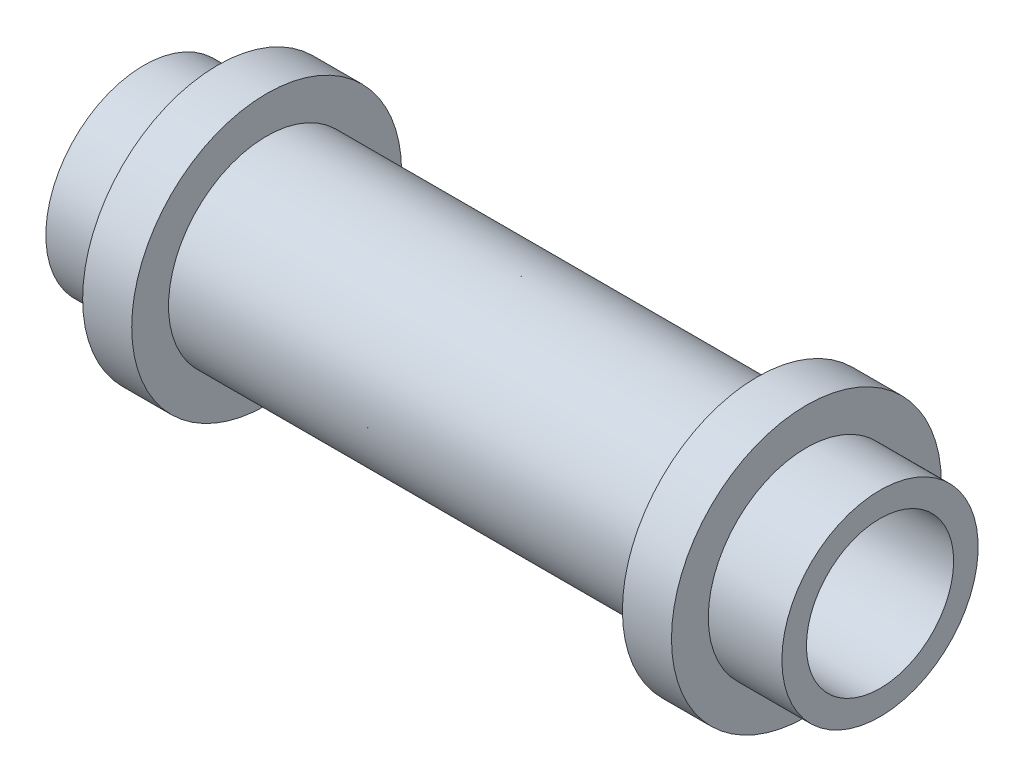
SolidWorks part; units mm, degrees
ref_plane "Front Plane" through (0, 0, 0) normal (0, 0, 1) x (1, 0, 0)
ref_plane "Top Plane" through (0, 0, 0) normal (0, 1, 0) x (1, 0, 0)
ref_plane "Right Plane" through (0, 0, 0) normal (1, 0, 0) x (0, 0, -1)
sketch "Sketch1" plane through (0, 0, 0) normal (1, 0, 0) x (0, 0, -1)
  circle A0 centre (0, 0) radius 8.7312
  dimension "D1" = 17.4625
extrude "Boss-Extrude1" add sketch "Sketch1" along normal blind 3.175
sketch "Sketch2" plane through (3.175, 0, 0) normal (1, 0, 0) x (0, 0, -1)
  circle A0 centre (0, 0) radius 6.35
  dimension "D1" = 12.7
extrude "Boss-Extrude2" add sketch "Sketch2" along normal blind 15.875
sketch "Sketch4" plane through (0, 0, 0) normal (-1, 0, 0) x (0, 0, 1)
  circle A0 centre (0, 0) radius 6.35
  dimension "D1" = 12.7
extrude "Boss-Extrude3" add sketch "Sketch4" along normal blind 4.7625
sketch "Sketch5" plane through (-4.7625, 0, 0) normal (-1, 0, 0) x (0, 0, 1)
  circle A0 centre (0, 0) radius 4.7625
  dimension "D1" = 9.525
extrude "Cut-Extrude1" cut sketch "Sketch5" against normal blind 508 contours A0
mirror "Mirror1" about plane through (19.05, 0, 0) normal (1, 0, 0) of "Cut-Extrude1", "Boss-Extrude3", "Boss-Extrude1", "Boss-Extrude2"
sketch "Sketch7" plane through (34.925, 0, 0) normal (1, 0, 0) x (0, 0, -1)
  circle A0 centre (0, 0) radius 8.7312
  dimension "D1" = 17.4625
extrude "Boss-Extrude4" add sketch "Sketch7" along normal blind 3.175
sketch "Sketch8" plane through (38.1, 0, 0) normal (1, 0, 0) x (0, 0, -1)
  circle A0 centre (0, 0) radius 4.7625
  circle A1 centre (0, 0) radius 6.35
  dimension "D1" = 12.7
  dimension "D2" = 9.525
extrude "Boss-Extrude5" add sketch "Sketch8" along normal blind 4.7625 contours A1
sketch "Sketch9" plane through (42.8625, 0, 0) normal (1, 0, 0) x (0, 0, -1)
  circle A0 centre (0, 0) radius 4.7625
extrude "Cut-Extrude2" cut sketch "Sketch9" against normal through all
